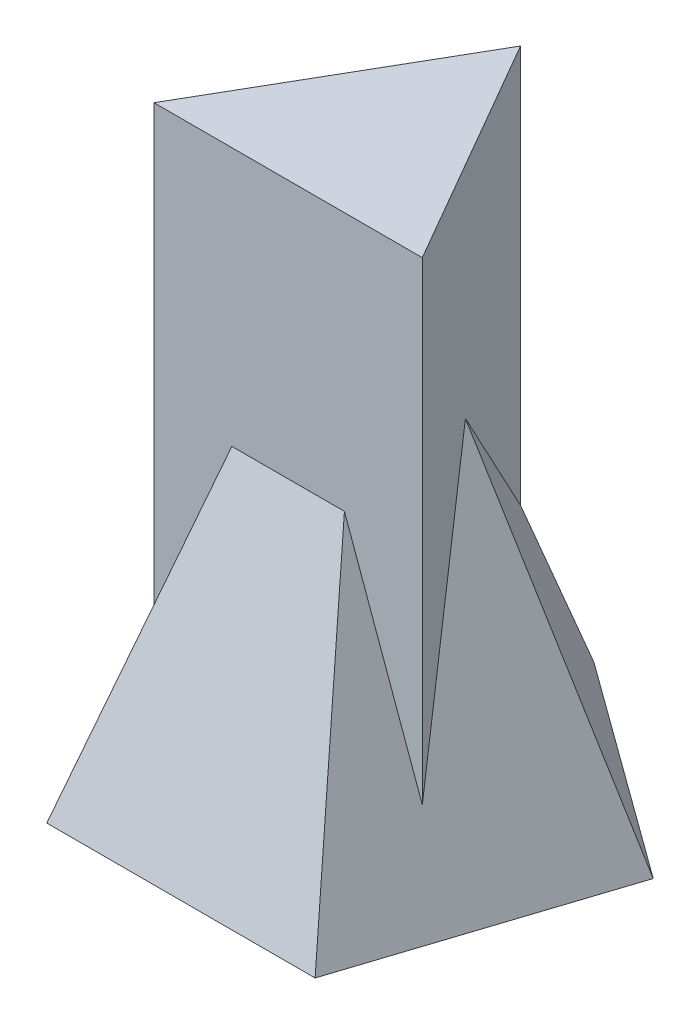
SolidWorks part; units mm, degrees
ref_plane "Front Plane" through (0, 0, 0) normal (0, 0, 1) x (1, 0, 0)
ref_plane "Top Plane" through (0, 0, 0) normal (0, 1, 0) x (1, 0, 0)
ref_plane "Right Plane" through (0, 0, 0) normal (1, 0, 0) x (0, 0, -1)
sketch "Sketch1" plane through (0, 0, 0) normal (0, 1, 0) x (1, 0, 0)
  line L1 (20, -27.5276) -> (32.3607, 10.5146)
  line L2 (32.3607, 10.5146) -> (0, 34.026)
  line L3 (0, 34.026) -> (-32.3607, 10.5146)
  line L4 (-32.3607, 10.5146) -> (-20, -27.5276)
  line L5 (-20, -27.5276) -> (20, -27.5276)
  circle A0 centre (0, 0) radius 27.5276 construction
  dimension "D1" = 40
ref_plane "Plane1" through (0, 80, 0) normal (0, 1, 0) x (1, 0, 0)
sketch "Sketch2" plane through (0, 80, 0) normal (0, 1, 0) x (1, 0, 0)
  point P0 (0, 0)
loft "Pyramid" add profiles "Sketch2", "Sketch1"
sketch "Sketch3" plane through (0, 0, 0) normal (0, 1, 0) x (1, 0, 0)
  line L0 (0, 0) -> (0, 34.026) construction
  line L1 (20, -11.547) -> (0, 23.094)
  line L2 (0, 23.094) -> (-20, -11.547)
  line L3 (-20, -11.547) -> (20, -11.547)
  circle A0 centre (0, 0) radius 11.547 construction
extrude "Triangular prism" add sketch "Sketch3" along normal blind 85
